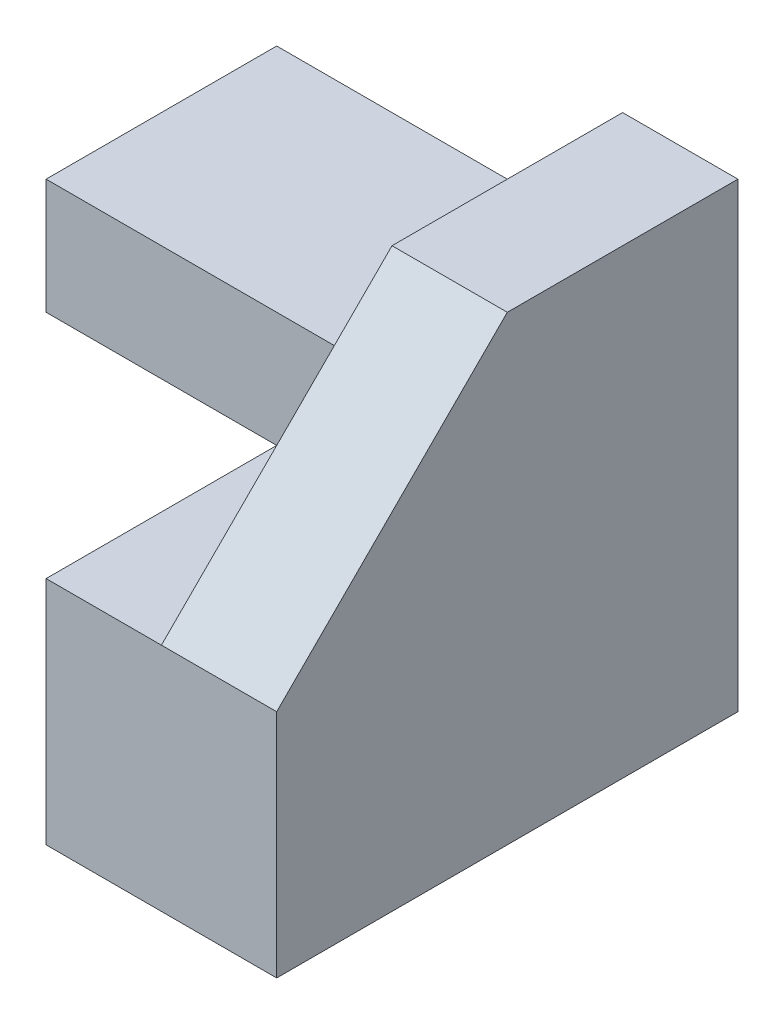
SolidWorks part; units mm, degrees
ref_plane "Front Plane" through (0, 0, 0) normal (0, 0, 1) x (1, 0, 0)
ref_plane "Top Plane" through (0, 0, 0) normal (0, 1, 0) x (1, 0, 0)
ref_plane "Right Plane" through (0, 0, 0) normal (1, 0, 0) x (0, 0, -1)
sketch "Sketch2" plane through (0, 0, 0) normal (0, 0, 1) x (1, 0, 0)
  line L1 (0, 0) -> (2, 0)
  line L2 (0, 0) -> (0, 2)
  line L3 (0, 2) -> (2, 2)
  line L4 (2, 0) -> (2, 2)
  dimension "D1" = 2
  dimension "D2" = 2
extrude "Boss-Extrude1" add sketch "Sketch2" along normal blind 4
sketch "Sketch3" plane through (0, 0, 0) normal (-1, 0, 0) x (0, 0, 1)
  line L0 (0, 1) -> (0, 3)
  line L1 (0, 2) -> (0, 0) construction
  line L2 (0, 3) -> (2, 3)
  line L3 (2, 3) -> (2, 2)
  line L4 (4, 2) -> (0, 2) construction
  line L5 (2, 2) -> (0, 1)
  dimension "D1" = 1
  dimension "D2" = 2
extrude "Boss-Extrude2" add sketch "Sketch3" along normal blind 2 and the other way blind 1
sketch "Sketch4" plane through (0, 2, 0) normal (0, 1, 0) x (1, 0, 0)
  line L0 (2, 0) -> (1, 0) construction
  line L1 (1, -2) -> (2, -2)
  line L2 (1, -2) -> (1, 0)
  line L3 (1, 0) -> (2, 0)
  line L4 (2, -2) -> (2, 0)
  line L5 (2, -4) -> (2, 0) construction
extrude "Boss-Extrude3" add sketch "Sketch4" along normal blind 2
sketch "Sketch5" plane through (2, 0, 0) normal (1, 0, 0) x (0, 0, -1)
  line L0 (-2, 4) -> (-4, 2)
  line L1 (-4, 2) -> (-2, 2)
  line L2 (-2, 2) -> (-2, 4)
extrude "Boss-Extrude4" add sketch "Sketch5" against normal blind 1
